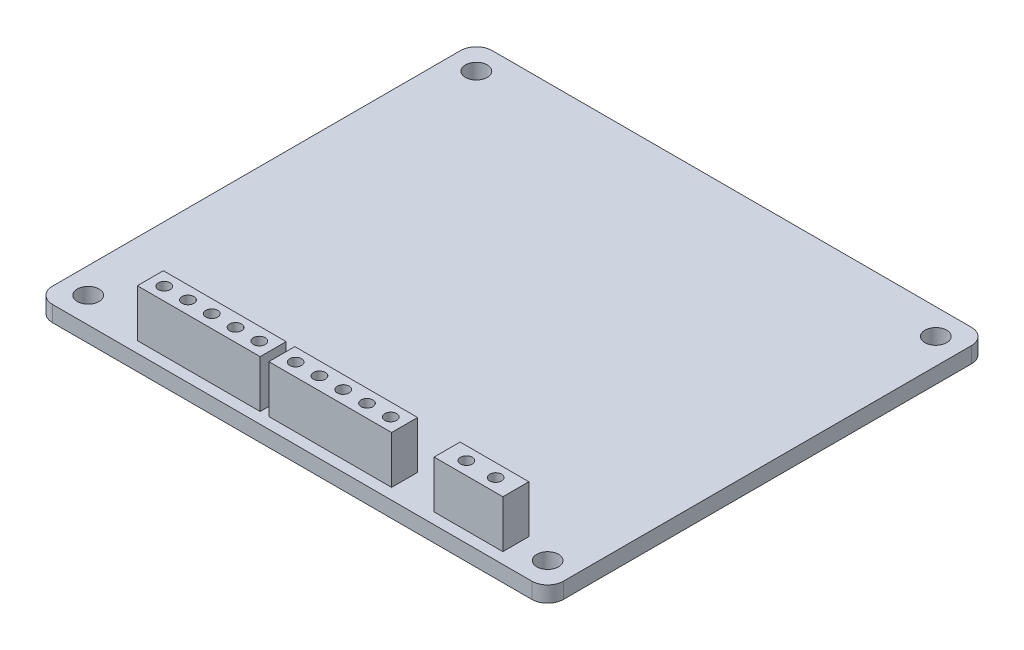
SolidWorks part; units mm, degrees
ref_plane "Front Plane" through (0, 0, 0) normal (0, 0, 1) x (1, 0, 0)
ref_plane "Top Plane" through (0, 0, 0) normal (0, 1, 0) x (1, 0, 0)
ref_plane "Right Plane" through (0, 0, 0) normal (1, 0, 0) x (0, 0, -1)
sketch "Sketch1" plane through (0, 0, 0) normal (0, 1, 0) x (1, 0, 0)
  line L1 (-32.25, -27.75) -> (32.25, -27.75)
  line L2 (-32.25, -27.75) -> (-32.25, 27.75)
  line L3 (-32.25, 27.75) -> (32.25, 27.75)
  line L4 (32.25, -27.75) -> (32.25, 27.75)
  line L5 (-32.25, -27.75) -> (32.25, 27.75) construction
  line L6 (-32.25, 27.75) -> (32.25, -27.75) construction
  point P0 (0, 0)
  dimension "D1" = 64.5
  dimension "D2" = 55.5
extrude "Boss-Extrude1" add sketch "Sketch1" along normal blind 2
fillet "Fillet1" radius 2 4 edges at (-32.25, 1, 27.75) (-32.25, 1, -27.75) (32.25, 1, -27.75) (32.25, 1, 27.75)
sketch "Sketch2" plane through (0, 2, 0) normal (0, 1, 0) x (1, 0, 0)
  line L0 (0, -24.5) -> (0, 24.5) construction
  line L1 (-29, 24.5) -> (29, 24.5) construction
  line L2 (-29, -24.5) -> (29, -24.5) construction
  circle A0 centre (-29, 24.5) radius 1.375
  circle A1 centre (29, 24.5) radius 1.375
  circle A2 centre (29, -24.5) radius 1.375
  circle A3 centre (-29, -24.5) radius 1.375
  point P4 (0, 0)
  point P8 (0, 24.5)
  point P10 (0, -24.5)
extrude "Cut-Extrude1" cut sketch "Sketch2" against normal blind 2
sketch "Sketch3" plane through (0, 2, 0) normal (0, 1, 0) x (1, 0, 0)
  line L1 (-20.9405, -26.3512) -> (-5.4405, -26.3512)
  line L2 (-20.9405, -26.3512) -> (-20.9405, -23.0684)
  line L3 (-20.9405, -23.0684) -> (-5.4405, -23.0684)
  line L4 (-5.4405, -26.3512) -> (-5.4405, -23.0684)
  line L5 (-4.3469, -23.0684) -> (11.1531, -23.0684)
  line L6 (-4.3469, -23.0684) -> (-4.3469, -26.3512)
  line L7 (-4.3469, -26.3512) -> (11.1531, -26.3512)
  line L8 (11.1531, -23.0684) -> (11.1531, -26.3512)
  line L9 (16.5188, -26.3512) -> (25.1978, -26.3512)
  line L10 (16.5188, -26.3512) -> (16.5188, -23.0684)
  line L11 (16.5188, -23.0684) -> (25.1978, -23.0684)
  line L12 (25.1978, -26.3512) -> (25.1978, -23.0684)
  dimension "D1" = 15.5
  dimension "D2" = 15.5
extrude "Boss-Extrude2" add sketch "Sketch3" along normal blind 6
sketch "Sketch4" plane through (0, 8, 0) normal (0, 1, 0) x (1, 0, 0)
  line L0 (-13.1905, -23.0684) -> (-13.1905, -26.3512) construction
  line L1 (-5.4405, -23.0684) -> (-20.9405, -23.0684) construction
  line L2 (-20.9405, -26.3512) -> (-5.4405, -26.3512) construction
  circle A0 centre (-13.1905, -24.7098) radius 0.75
extrude "Cut-Extrude2" cut sketch "Sketch4" against normal blind 3
pattern_linear "LPattern1" count 3 spacing 3 along (-1, 0, 0) count 3 spacing 3 along (1, 0, 0) of "Cut-Extrude2"
sketch "Sketch5" plane through (0, 8, 0) normal (0, 1, 0) x (1, 0, 0)
  line L0 (3.4031, -23.0684) -> (3.4031, -26.3512) construction
  line L1 (11.1531, -23.0684) -> (-4.3469, -23.0684) construction
  line L2 (-4.3469, -26.3512) -> (11.1531, -26.3512) construction
  circle A0 centre (3.4031, -24.7098) radius 0.75
extrude "Cut-Extrude3" cut sketch "Sketch5" against normal blind 3
pattern_linear "LPattern2" count 3 spacing 3 along (-1, 0, 0) count 3 spacing 3 along (1, 0, 0) of "Cut-Extrude3"
sketch "Sketch6" plane through (0, 8, 0) normal (0, 1, 0) x (1, 0, 0)
  line L0 (18.9457, -23.0684) -> (18.9457, -26.3512) construction
  line L1 (25.1978, -23.0684) -> (16.5188, -23.0684) construction
  line L2 (16.5188, -26.3512) -> (25.1978, -26.3512) construction
  circle A0 centre (18.9457, -24.7098) radius 0.75
extrude "Cut-Extrude4" cut sketch "Sketch6" against normal blind 3
pattern_linear "LPattern3" count 2 spacing 3.7 along (1, 0, 0) of "Cut-Extrude4"
